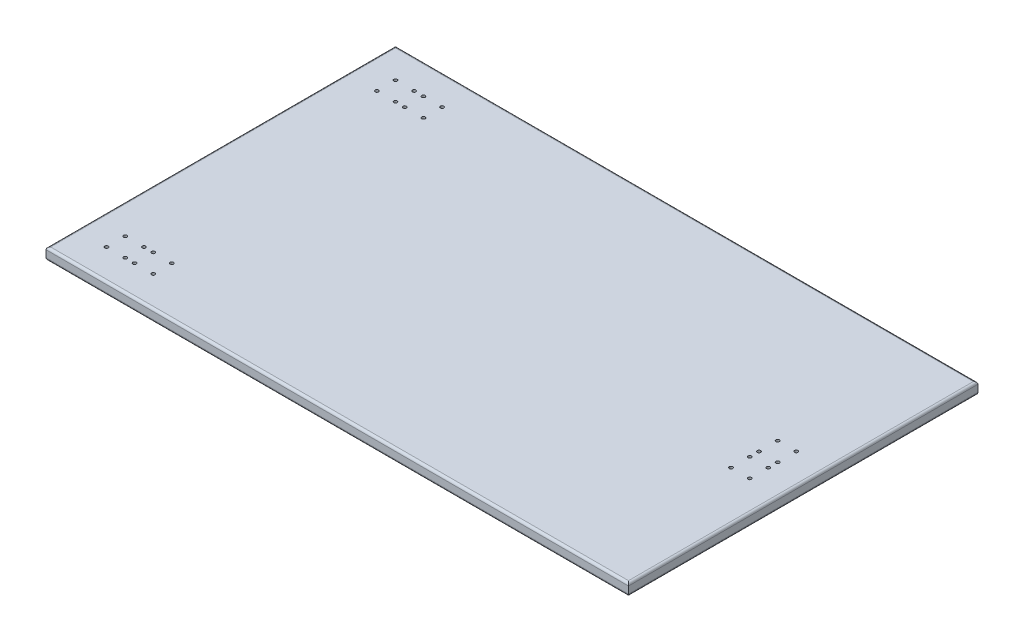
SolidWorks part; units mm, degrees
ref_plane "Plan de face" through (0, 0, 0) normal (0, 0, 1) x (1, 0, 0)
ref_plane "Plan de dessus" through (0, 0, 0) normal (0, 1, 0) x (1, 0, 0)
ref_plane "Plan de droite" through (0, 0, 0) normal (1, 0, 0) x (0, 0, -1)
sketch "Esquisse1" plane through (0, 0, 0) normal (0, 1, 0) x (1, 0, 0)
  line L1 (1250, -750) -> (-1250, -750)
  line L2 (1250, -750) -> (1250, 750)
  line L3 (1250, 750) -> (-1250, 750)
  line L4 (-1250, -750) -> (-1250, 750)
  line L5 (1250, -750) -> (-1250, 750) construction
  line L6 (1250, 750) -> (-1250, -750) construction
  point P0 (0, 0)
  dimension "D1" = 1500
  dimension "D2" = 2500
extrude "Boss.-Extru.1" add sketch "Esquisse1" along normal blind 50
fillet "Congé1" radius 10 4 edges at (0, 50, -750) (1250, 50, 0) (0, 50, 750) (-1250, 50, 0)
fillet "Congé2" radius 10 4 edges at (0, 0, 750) (1250, 0, 0) (0, 0, -750) (-1250, 0, 0)
sketch "Esquisse4" plane through (0, 0, 0) normal (0, -1, 0) x (1, 0, 0)
  line L0 (-1000, 0) -> (49000, 0) construction
  line L1 (1140, -1000) -> (1140, 49000) construction
  line L2 (1240, -740) -> (1240, 740) construction
  line L3 (140, -120) -> (50140, -120) construction
  line L5 (1020, -1000) -> (1020, 49000) construction
  line L6 (1080, -1000) -> (1080, 49000) construction
  line L7 (82.8838, -60) -> (50082.8838, -60) construction
  circle A0 centre (1120, -100) radius 7.25
  circle A1 centre (1040, -100) radius 7.25
  circle A2 centre (1040, -20) radius 7.25
  circle A3 centre (1120, -20) radius 7.25
  circle A4 centre (1120, 100) radius 7.25
  circle A5 centre (1120, 20) radius 7.25
  circle A6 centre (1040, 20) radius 7.25
  circle A7 centre (1040, 100) radius 7.25
  dimension "D6" = 14.5
  dimension "D1" = 100
  dimension "D2" = 120
  dimension "D3" = 120
  dimension "D4" = 20
  dimension "D5" = 20
  dimension "D7" = 20
  dimension "D8" = 20
  dimension "D9" = 20
  dimension "D10" = 20
  dimension "D11" = 20
  dimension "D12" = 20
extrude "Enlèv. mat.-Extru.2" cut sketch "Esquisse4" against normal through all
sketch "Esquisse5" plane through (0, 0, 0) normal (0, -1, 0) x (-1, 0, 0)
  line L0 (-1000, 0) -> (49000, 0) construction
  line L1 (1140, -1000) -> (1140, 49000) construction
  line L2 (1240, -740) -> (1240, 740) construction
  line L3 (140, 640) -> (50140, 640) construction
  line L4 (1240, 740) -> (-1240, 740) construction
  line L5 (1020, -360) -> (1020, 49640) construction
  line L6 (140, 580) -> (50140, 580) construction
  line L7 (1080, -420) -> (1080, 49580) construction
  circle A0 centre (1120, 620) radius 7.25
  circle A1 centre (1040, 620) radius 7.25
  circle A2 centre (1040, 540) radius 7.25
  circle A3 centre (1120, 540) radius 7.25
  circle A4 centre (920, 620) radius 7.25
  circle A5 centre (1000, 620) radius 7.25
  circle A6 centre (1000, 540) radius 7.25
  circle A7 centre (920, 540) radius 7.25
  circle A8 centre (920, -620) radius 7.25
  circle A9 centre (920, -540) radius 7.25
  circle A10 centre (1000, -540) radius 7.25
  circle A11 centre (1000, -620) radius 7.25
  circle A12 centre (1040, -620) radius 7.25
  circle A13 centre (1040, -540) radius 7.25
  circle A14 centre (1120, -540) radius 7.25
  circle A15 centre (1120, -620) radius 7.25
  dimension "D4" = 14.5
  dimension "D1" = 100
  dimension "D2" = 100
  dimension "D3" = 120
  dimension "D5" = 20
  dimension "D6" = 20
  dimension "D7" = 60
  dimension "D8" = 60
extrude "Enlèv. mat.-Extru.3" cut sketch "Esquisse5" against normal through all
